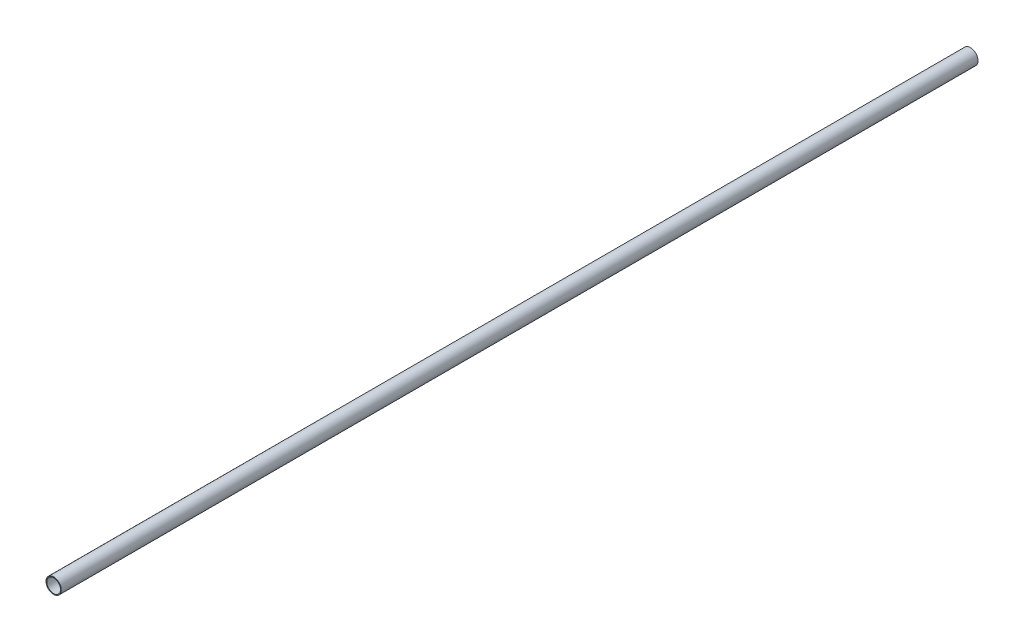
SolidWorks part; units mm, degrees
material "carbon fiber"
ref_plane "Front Plane" through (0, 0, 0) normal (0, 0, 1) x (1, 0, 0)
ref_plane "Top Plane" through (0, 0, 0) normal (0, 1, 0) x (1, 0, 0)
ref_plane "Right Plane" through (0, 0, 0) normal (1, 0, 0) x (0, 0, -1)
sketch "Эскиз1" plane through (0, 0, 0) normal (0, 0, 1) x (1, 0, 0)
  circle A0 centre (0, 0) radius 10
  circle A1 centre (0, 0) radius 9
  dimension "D1" = 20
  dimension "D2" = 1
extrude "Бобышка-Вытянуть1" add sketch "Эскиз1" along normal mid plane 1200
